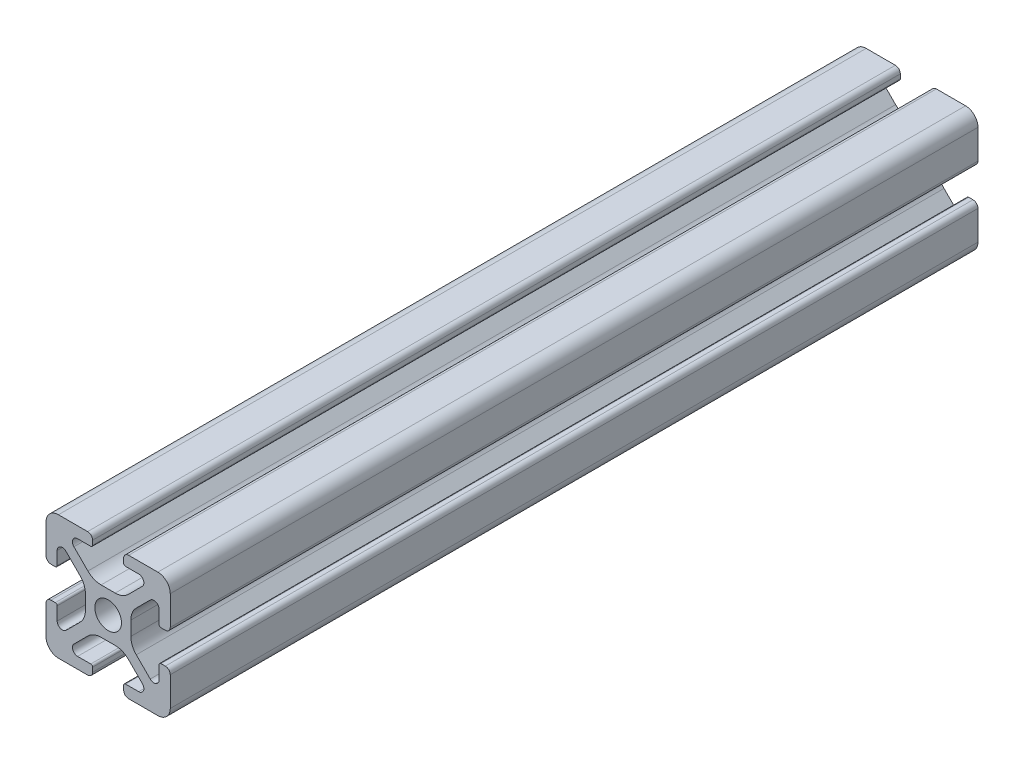
SolidWorks part; units mm, degrees
ref_plane "Front" through (0, 0, 0) normal (0, 0, 1) x (1, 0, 0)
ref_plane "Top" through (0, 0, 0) normal (0, 1, 0) x (1, 0, 0)
ref_plane "Right" through (0, 0, 0) normal (1, 0, 0) x (0, 0, -1)
sketch "Support-Front" plane through (0, 0, 0) normal (0, 0, 1) x (1, 0, 0)
  line L0 (10, 0) -> (-10, 0) construction
  line L1 (-10, -10) -> (10, -10)
  line L2 (-10, -10) -> (-10, 10)
  line L3 (-10, 10) -> (10, 10)
  line L4 (10, -10) -> (10, 10)
  line L5 (0, 10) -> (0, -10) construction
  dimension "Height-Profile" = 20
  dimension "Width-Profile" = 20
sketch "Support-Right-Length" plane through (0, 0, 0) normal (1, 0, 0) x (0, 0, -1)
  line L0 (0, -10) -> (0, 10) construction
  line L1 (-25, 10) -> (25, 10)
  line L2 (-25, 10) -> (-25, -10)
  line L3 (-25, -10) -> (25, -10)
  line L4 (25, 10) -> (25, -10)
  dimension "Length-Profile" = 50
sketch "Support-Profile" plane through (0, 0, 0) normal (0, 0, 1) x (1, 0, 0)
  line L8 (4.9176, -8.2) -> (2.8, -8.2)
  line L9 (2.5, -8.5) -> (2.5, -9.2)
  line L10 (3.3, -10) -> (8, -10)
  line L11 (10, -8) -> (10, -3.3)
  line L24 (9.2, -2.5) -> (8.5, -2.5)
  line L25 (8.2, -2.8) -> (8.2, -4.9176)
  line L26 (6.779, -5.5062) -> (4.5287, -3.2559)
  line L27 (3.65, -1.1346) -> (3.65, 1.1346)
  line L28 (4.5287, 3.2559) -> (6.779, 5.5062)
  line L29 (8.2, 4.9176) -> (8.2, 2.8)
  line L30 (8.5, 2.5) -> (9.2, 2.5)
  line L31 (10, 3.3) -> (10, 8)
  line L32 (8, 10) -> (3.3, 10)
  line L33 (2.5, 9.2) -> (2.5, 8.5)
  line L34 (2.8, 8.2) -> (4.9176, 8.2)
  line L35 (5.5062, 6.779) -> (3.2559, 4.5287)
  line L40 (1.1346, 3.65) -> (-1.1346, 3.65)
  line L41 (-3.2559, 4.5287) -> (-5.5062, 6.779)
  line L42 (-4.9176, 8.2) -> (-2.8, 8.2)
  line L43 (-2.5, 8.5) -> (-2.5, 9.2)
  line L44 (-3.3, 10) -> (-8, 10)
  line L45 (-10, 8) -> (-10, 3.3)
  line L46 (-9.2, 2.5) -> (-8.5, 2.5)
  line L47 (-8.2, 2.8) -> (-8.2, 4.9176)
  line L48 (-6.779, 5.5062) -> (-4.5287, 3.2559)
  line L49 (-3.65, 1.1346) -> (-3.65, -1.1346)
  line L50 (-4.5287, -3.2559) -> (-6.779, -5.5062)
  line L51 (-8.2, -4.9176) -> (-8.2, -2.8)
  line L52 (-8.5, -2.5) -> (-9.2, -2.5)
  line L53 (-10, -3.3) -> (-10, -8)
  line L54 (-8, -10) -> (-3.3, -10)
  line L55 (-2.5, -9.2) -> (-2.5, -8.5)
  line L56 (-2.8, -8.2) -> (-4.9176, -8.2)
  line L57 (-5.5062, -6.779) -> (-3.2559, -4.5287)
  line L58 (-1.1346, -3.65) -> (1.1346, -3.65)
  line L59 (3.2559, -4.5287) -> (5.5062, -6.779)
  circle A2 centre (0, 0) radius 2.15
  arc A3 (2.8, -8.2) -> (2.5, -8.5) centre (2.8, -8.5) ccw
  arc A5 (2.5, -9.2) -> (3.3, -10) centre (3.3, -9.2) ccw
  arc A24 (8, -10) -> (10, -8) centre (8, -8) ccw
  arc A25 (10, -3.3) -> (9.2, -2.5) centre (9.2, -3.3) ccw
  arc A26 (8.5, -2.5) -> (8.2, -2.8) centre (8.5, -2.8) ccw
  arc A27 (6.779, -5.5062) -> (8.2, -4.9176) centre (7.3676, -4.9176) ccw
  arc A28 (3.65, -1.1346) -> (4.5287, -3.2559) centre (6.65, -1.1346) ccw
  arc A29 (4.5287, 3.2559) -> (3.65, 1.1346) centre (6.65, 1.1346) ccw
  arc A30 (8.2, 4.9176) -> (6.779, 5.5062) centre (7.3676, 4.9176) ccw
  arc A31 (8.2, 2.8) -> (8.5, 2.5) centre (8.5, 2.8) ccw
  arc A32 (9.2, 2.5) -> (10, 3.3) centre (9.2, 3.3) ccw
  arc A33 (10, 8) -> (8, 10) centre (8, 8) ccw
  arc A34 (3.3, 10) -> (2.5, 9.2) centre (3.3, 9.2) ccw
  arc A35 (2.5, 8.5) -> (2.8, 8.2) centre (2.8, 8.5) ccw
  arc A38 (5.5062, 6.779) -> (4.9176, 8.2) centre (4.9176, 7.3676) ccw
  arc A39 (1.1346, 3.65) -> (3.2559, 4.5287) centre (1.1346, 6.65) ccw
  arc A44 (-3.2559, 4.5287) -> (-1.1346, 3.65) centre (-1.1346, 6.65) ccw
  arc A45 (-4.9176, 8.2) -> (-5.5062, 6.779) centre (-4.9176, 7.3676) ccw
  arc A46 (-2.8, 8.2) -> (-2.5, 8.5) centre (-2.8, 8.5) ccw
  arc A47 (-2.5, 9.2) -> (-3.3, 10) centre (-3.3, 9.2) ccw
  arc A48 (-8, 10) -> (-10, 8) centre (-8, 8) ccw
  arc A49 (-10, 3.3) -> (-9.2, 2.5) centre (-9.2, 3.3) ccw
  arc A50 (-8.5, 2.5) -> (-8.2, 2.8) centre (-8.5, 2.8) ccw
  arc A51 (-6.779, 5.5062) -> (-8.2, 4.9176) centre (-7.3676, 4.9176) ccw
  arc A52 (-3.65, 1.1346) -> (-4.5287, 3.2559) centre (-6.65, 1.1346) ccw
  arc A53 (-4.5287, -3.2559) -> (-3.65, -1.1346) centre (-6.65, -1.1346) ccw
  arc A54 (-8.2, -4.9176) -> (-6.779, -5.5062) centre (-7.3676, -4.9176) ccw
  arc A55 (-8.2, -2.8) -> (-8.5, -2.5) centre (-8.5, -2.8) ccw
  arc A56 (-9.2, -2.5) -> (-10, -3.3) centre (-9.2, -3.3) ccw
  arc A57 (-10, -8) -> (-8, -10) centre (-8, -8) ccw
  arc A58 (-3.3, -10) -> (-2.5, -9.2) centre (-3.3, -9.2) ccw
  arc A59 (-2.5, -8.5) -> (-2.8, -8.2) centre (-2.8, -8.5) ccw
  arc A60 (-5.5062, -6.779) -> (-4.9176, -8.2) centre (-4.9176, -7.3676) ccw
  arc A61 (-1.1346, -3.65) -> (-3.2559, -4.5287) centre (-1.1346, -6.65) ccw
  arc A62 (3.2559, -4.5287) -> (1.1346, -3.65) centre (1.1346, -6.65) ccw
  arc A63 (4.9176, -8.2) -> (5.5062, -6.779) centre (4.9176, -7.3676) ccw
ref_plane "Ref-Plane-1" through (0, 0, 25) normal (0, 0, 1) x (1, 0, 0)
ref_plane "Ref-Plane-2" through (0, 0, -25) normal (0, 0, 1) x (1, 0, 0)
sketch "Sketch4" plane through (0, 0, 25) normal (0, 0, 1) x (1, 0, 0)
  line L0 (-10, -10) -> (-10, 10) construction
  line L1 (-10, -10) -> (10, -10) construction
  line L2 (10, -10) -> (10, 10) construction
  line L3 (-10, 10) -> (10, 10) construction
  line L4 (-10, -10) -> (-10, 10)
  line L5 (-10, -10) -> (10, -10)
  line L6 (10, -10) -> (10, 10)
  line L7 (-10, 10) -> (10, 10)
extrude "Body" add sketch "Sketch4" against normal blind 130
sketch "Sketch16" plane through (0, 0, 0) normal (0, 0, 1) x (1, 0, 0)
  line L40 (4.9176, -8.2) -> (2.8, -8.2)
  line L41 (2.5, -8.5) -> (2.5, -9.2)
  line L42 (3.3, -10) -> (8, -10)
  line L43 (10, -8) -> (10, -3.3)
  line L44 (9.2, -2.5) -> (8.5, -2.5)
  line L45 (8.2, -2.8) -> (8.2, -4.9176)
  line L46 (6.779, -5.5062) -> (4.5287, -3.2559)
  line L47 (3.65, -1.1346) -> (3.65, 1.1346)
  line L48 (4.5287, 3.2559) -> (6.779, 5.5062)
  line L49 (8.2, 4.9176) -> (8.2, 2.8)
  line L50 (8.5, 2.5) -> (9.2, 2.5)
  line L51 (10, 3.3) -> (10, 8)
  line L52 (8, 10) -> (3.3, 10)
  line L53 (2.5, 9.2) -> (2.5, 8.5)
  line L54 (2.8, 8.2) -> (4.9176, 8.2)
  line L55 (5.5062, 6.779) -> (3.2559, 4.5287)
  line L56 (1.1346, 3.65) -> (-1.1346, 3.65)
  line L57 (-3.2559, 4.5287) -> (-5.5062, 6.779)
  line L58 (-4.9176, 8.2) -> (-2.8, 8.2)
  line L59 (-2.5, 8.5) -> (-2.5, 9.2)
  line L60 (-3.3, 10) -> (-8, 10)
  line L61 (-10, 8) -> (-10, 3.3)
  line L62 (-9.2, 2.5) -> (-8.5, 2.5)
  line L63 (-8.2, 2.8) -> (-8.2, 4.9176)
  line L64 (-6.779, 5.5062) -> (-4.5287, 3.2559)
  line L65 (-3.65, 1.1346) -> (-3.65, -1.1346)
  line L66 (-4.5287, -3.2559) -> (-6.779, -5.5062)
  line L67 (-8.2, -4.9176) -> (-8.2, -2.8)
  line L68 (-8.5, -2.5) -> (-9.2, -2.5)
  line L69 (-10, -3.3) -> (-10, -8)
  line L70 (-8, -10) -> (-3.3, -10)
  line L71 (-2.5, -9.2) -> (-2.5, -8.5)
  line L72 (-2.8, -8.2) -> (-4.9176, -8.2)
  line L73 (-5.5062, -6.779) -> (-3.2559, -4.5287)
  line L74 (-1.1346, -3.65) -> (1.1346, -3.65)
  line L75 (3.2559, -4.5287) -> (5.5062, -6.779)
  line L76 (4.9176, -8.2) -> (2.8, -8.2)
  line L77 (2.5, -8.5) -> (2.5, -9.2)
  line L78 (3.3, -10) -> (8, -10)
  line L79 (10, -8) -> (10, -3.3)
  line L80 (9.2, -2.5) -> (8.5, -2.5)
  line L81 (8.2, -2.8) -> (8.2, -4.9176)
  line L82 (6.779, -5.5062) -> (4.5287, -3.2559)
  line L83 (3.65, -1.1346) -> (3.65, 1.1346)
  line L84 (4.5287, 3.2559) -> (6.779, 5.5062)
  line L85 (8.2, 4.9176) -> (8.2, 2.8)
  line L86 (8.5, 2.5) -> (9.2, 2.5)
  line L87 (10, 3.3) -> (10, 8)
  line L88 (8, 10) -> (3.3, 10)
  line L89 (2.5, 9.2) -> (2.5, 8.5)
  line L90 (2.8, 8.2) -> (4.9176, 8.2)
  line L91 (5.5062, 6.779) -> (3.2559, 4.5287)
  line L92 (1.1346, 3.65) -> (-1.1346, 3.65)
  line L93 (-3.2559, 4.5287) -> (-5.5062, 6.779)
  line L94 (-4.9176, 8.2) -> (-2.8, 8.2)
  line L95 (-2.5, 8.5) -> (-2.5, 9.2)
  line L96 (-3.3, 10) -> (-8, 10)
  line L97 (-10, 8) -> (-10, 3.3)
  line L98 (-9.2, 2.5) -> (-8.5, 2.5)
  line L99 (-8.2, 2.8) -> (-8.2, 4.9176)
  line L100 (-6.779, 5.5062) -> (-4.5287, 3.2559)
  line L101 (-3.65, 1.1346) -> (-3.65, -1.1346)
  line L102 (-4.5287, -3.2559) -> (-6.779, -5.5062)
  line L103 (-8.2, -4.9176) -> (-8.2, -2.8)
  line L104 (-8.5, -2.5) -> (-9.2, -2.5)
  line L105 (-10, -3.3) -> (-10, -8)
  line L106 (-8, -10) -> (-3.3, -10)
  line L107 (-2.5, -9.2) -> (-2.5, -8.5)
  line L108 (-2.8, -8.2) -> (-4.9176, -8.2)
  line L109 (-5.5062, -6.779) -> (-3.2559, -4.5287)
  line L110 (-1.1346, -3.65) -> (1.1346, -3.65)
  line L111 (3.2559, -4.5287) -> (5.5062, -6.779)
  circle A7 centre (0, 0) radius 2.15 construction
  circle A8 centre (0, 0) radius 2.15
  arc A43 (2.8, -8.2) -> (2.5, -8.5) centre (2.8, -8.5) ccw
  arc A44 (2.5, -9.2) -> (3.3, -10) centre (3.3, -9.2) ccw
  arc A45 (8, -10) -> (10, -8) centre (8, -8) ccw
  arc A46 (10, -3.3) -> (9.2, -2.5) centre (9.2, -3.3) ccw
  arc A47 (8.5, -2.5) -> (8.2, -2.8) centre (8.5, -2.8) ccw
  arc A48 (6.779, -5.5062) -> (8.2, -4.9176) centre (7.3676, -4.9176) ccw
  arc A49 (3.65, -1.1346) -> (4.5287, -3.2559) centre (6.65, -1.1346) ccw
  arc A50 (4.5287, 3.2559) -> (3.65, 1.1346) centre (6.65, 1.1346) ccw
  arc A51 (8.2, 4.9176) -> (6.779, 5.5062) centre (7.3676, 4.9176) ccw
  arc A52 (8.2, 2.8) -> (8.5, 2.5) centre (8.5, 2.8) ccw
  arc A53 (9.2, 2.5) -> (10, 3.3) centre (9.2, 3.3) ccw
  arc A54 (10, 8) -> (8, 10) centre (8, 8) ccw
  arc A55 (3.3, 10) -> (2.5, 9.2) centre (3.3, 9.2) ccw
  arc A56 (2.5, 8.5) -> (2.8, 8.2) centre (2.8, 8.5) ccw
  arc A57 (5.5062, 6.779) -> (4.9176, 8.2) centre (4.9176, 7.3676) ccw
  arc A58 (1.1346, 3.65) -> (3.2559, 4.5287) centre (1.1346, 6.65) ccw
  arc A59 (-3.2559, 4.5287) -> (-1.1346, 3.65) centre (-1.1346, 6.65) ccw
  arc A60 (-4.9176, 8.2) -> (-5.5062, 6.779) centre (-4.9176, 7.3676) ccw
  arc A61 (-2.8, 8.2) -> (-2.5, 8.5) centre (-2.8, 8.5) ccw
  arc A62 (-2.5, 9.2) -> (-3.3, 10) centre (-3.3, 9.2) ccw
  arc A63 (-8, 10) -> (-10, 8) centre (-8, 8) ccw
  arc A64 (-10, 3.3) -> (-9.2, 2.5) centre (-9.2, 3.3) ccw
  arc A65 (-8.5, 2.5) -> (-8.2, 2.8) centre (-8.5, 2.8) ccw
  arc A66 (-6.779, 5.5062) -> (-8.2, 4.9176) centre (-7.3676, 4.9176) ccw
  arc A67 (-3.65, 1.1346) -> (-4.5287, 3.2559) centre (-6.65, 1.1346) ccw
  arc A68 (-4.5287, -3.2559) -> (-3.65, -1.1346) centre (-6.65, -1.1346) ccw
  arc A69 (-8.2, -4.9176) -> (-6.779, -5.5062) centre (-7.3676, -4.9176) ccw
  arc A70 (-8.2, -2.8) -> (-8.5, -2.5) centre (-8.5, -2.8) ccw
  arc A71 (-9.2, -2.5) -> (-10, -3.3) centre (-9.2, -3.3) ccw
  arc A72 (-10, -8) -> (-8, -10) centre (-8, -8) ccw
  arc A73 (-3.3, -10) -> (-2.5, -9.2) centre (-3.3, -9.2) ccw
  arc A74 (-2.5, -8.5) -> (-2.8, -8.2) centre (-2.8, -8.5) ccw
  arc A75 (-5.5062, -6.779) -> (-4.9176, -8.2) centre (-4.9176, -7.3676) ccw
  arc A76 (-1.1346, -3.65) -> (-3.2559, -4.5287) centre (-1.1346, -6.65) ccw
  arc A77 (3.2559, -4.5287) -> (1.1346, -3.65) centre (1.1346, -6.65) ccw
  arc A78 (4.9176, -8.2) -> (5.5062, -6.779) centre (4.9176, -7.3676) ccw
  arc A79 (2.8, -8.2) -> (2.5, -8.5) centre (2.8, -8.5) ccw
  arc A80 (2.5, -9.2) -> (3.3, -10) centre (3.3, -9.2) ccw
  arc A81 (8, -10) -> (10, -8) centre (8, -8) ccw
  arc A82 (10, -3.3) -> (9.2, -2.5) centre (9.2, -3.3) ccw
  arc A83 (8.5, -2.5) -> (8.2, -2.8) centre (8.5, -2.8) ccw
  arc A84 (6.779, -5.5062) -> (8.2, -4.9176) centre (7.3676, -4.9176) ccw
  arc A85 (3.65, -1.1346) -> (4.5287, -3.2559) centre (6.65, -1.1346) ccw
  arc A86 (4.5287, 3.2559) -> (3.65, 1.1346) centre (6.65, 1.1346) ccw
  arc A87 (8.2, 4.9176) -> (6.779, 5.5062) centre (7.3676, 4.9176) ccw
  arc A88 (8.2, 2.8) -> (8.5, 2.5) centre (8.5, 2.8) ccw
  arc A89 (9.2, 2.5) -> (10, 3.3) centre (9.2, 3.3) ccw
  arc A90 (10, 8) -> (8, 10) centre (8, 8) ccw
  arc A91 (3.3, 10) -> (2.5, 9.2) centre (3.3, 9.2) ccw
  arc A92 (2.5, 8.5) -> (2.8, 8.2) centre (2.8, 8.5) ccw
  arc A93 (5.5062, 6.779) -> (4.9176, 8.2) centre (4.9176, 7.3676) ccw
  arc A94 (1.1346, 3.65) -> (3.2559, 4.5287) centre (1.1346, 6.65) ccw
  arc A95 (-3.2559, 4.5287) -> (-1.1346, 3.65) centre (-1.1346, 6.65) ccw
  arc A96 (-4.9176, 8.2) -> (-5.5062, 6.779) centre (-4.9176, 7.3676) ccw
  arc A97 (-2.8, 8.2) -> (-2.5, 8.5) centre (-2.8, 8.5) ccw
  arc A98 (-2.5, 9.2) -> (-3.3, 10) centre (-3.3, 9.2) ccw
  arc A99 (-8, 10) -> (-10, 8) centre (-8, 8) ccw
  arc A100 (-10, 3.3) -> (-9.2, 2.5) centre (-9.2, 3.3) ccw
  arc A101 (-8.5, 2.5) -> (-8.2, 2.8) centre (-8.5, 2.8) ccw
  arc A102 (-6.779, 5.5062) -> (-8.2, 4.9176) centre (-7.3676, 4.9176) ccw
  arc A103 (-3.65, 1.1346) -> (-4.5287, 3.2559) centre (-6.65, 1.1346) ccw
  arc A104 (-4.5287, -3.2559) -> (-3.65, -1.1346) centre (-6.65, -1.1346) ccw
  arc A105 (-8.2, -4.9176) -> (-6.779, -5.5062) centre (-7.3676, -4.9176) ccw
  arc A106 (-8.2, -2.8) -> (-8.5, -2.5) centre (-8.5, -2.8) ccw
  arc A107 (-9.2, -2.5) -> (-10, -3.3) centre (-9.2, -3.3) ccw
  arc A108 (-10, -8) -> (-8, -10) centre (-8, -8) ccw
  arc A109 (-3.3, -10) -> (-2.5, -9.2) centre (-3.3, -9.2) ccw
  arc A110 (-2.5, -8.5) -> (-2.8, -8.2) centre (-2.8, -8.5) ccw
  arc A111 (-5.5062, -6.779) -> (-4.9176, -8.2) centre (-4.9176, -7.3676) ccw
  arc A112 (-1.1346, -3.65) -> (-3.2559, -4.5287) centre (-1.1346, -6.65) ccw
  arc A113 (3.2559, -4.5287) -> (1.1346, -3.65) centre (1.1346, -6.65) ccw
  arc A114 (4.9176, -8.2) -> (5.5062, -6.779) centre (4.9176, -7.3676) ccw
  dimension "D1" = 0
extrude "Cut-Profile" cut sketch "Sketch16" against normal through all and the other way through all flip side to cut
